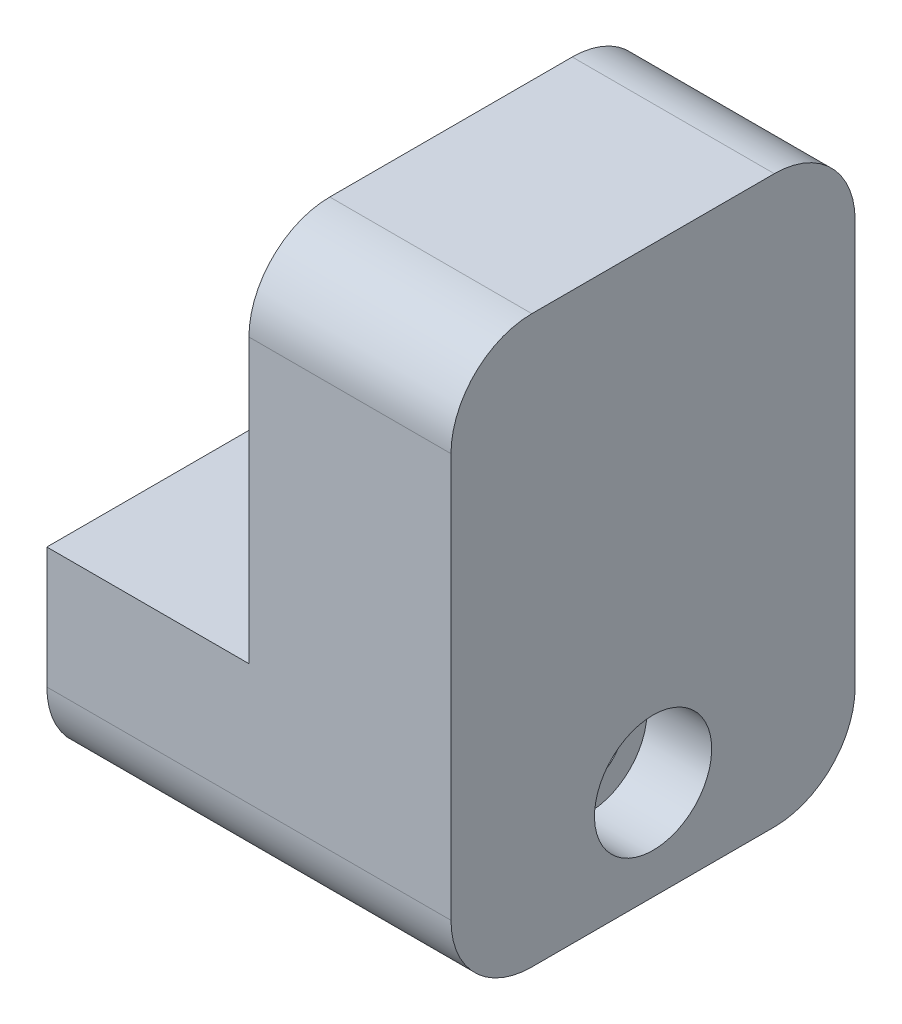
SolidWorks part; units mm, degrees
ref_plane "Front Plane" through (0, 0, 0) normal (0, 0, 1) x (1, 0, 0)
ref_plane "Top Plane" through (0, 0, 0) normal (0, 1, 0) x (1, 0, 0)
ref_plane "Right Plane" through (0, 0, 0) normal (1, 0, 0) x (0, 0, -1)
sketch "Profile" plane through (0, 0, 0) normal (0, 0, 1) x (1, 0, 0)
  line L1 (-6.35, 22.86) -> (6.35, 22.86)
  line L2 (-6.35, 22.86) -> (-6.35, 0)
  line L3 (-6.35, 0) -> (6.35, 0)
  line L4 (6.35, 22.86) -> (6.35, 0)
  line L5 (0, 0) -> (6.35, 0)
  line L6 (0, 0) -> (0, -12.7)
  line L7 (0, -12.7) -> (6.35, -12.7)
  line L8 (6.35, 0) -> (6.35, -12.7)
  dimension "D1" = 22.86
  dimension "D2" = 12.7
  dimension "D3" = 6.35
  dimension "D4" = 12.7
extrude "Boss-Extrude1" add sketch "Profile" along normal mid plane 25.4 contours L4 L1 L2 L3 | L8 L3 L6 L7
sketch "Sketch7" plane through (0, 0, 12.7) normal (0, 0, 1) x (1, 0, 0)
  line L0 (0, -12.7) -> (6.35, -12.7) construction
  line L1 (0, 0) -> (-19.05, 0)
  line L2 (0, 0) -> (0, -12.7)
  line L3 (0, -12.7) -> (-19.05, -12.7)
  line L4 (-19.05, 0) -> (-19.05, -12.7)
  line L5 (-6.35, 22.86) -> (-6.35, 0) construction
  dimension "D1" = 12.7
extrude "Boss-Extrude2" add sketch "Sketch7" against normal up to surface (25.4 mm away)
sketch "ScrewHole" plane through (-19.05, 0, 0) normal (-1, 0, 0) x (0, 0, 1)
  line L0 (-12.7, 0) -> (12.7, 0) construction
  circle A0 centre (0, -6.477) radius 2.159
  dimension "D1" = 4.318
  dimension "D2" = 6.477
extrude "Cut-Extrude1" cut sketch "ScrewHole" against normal through all both and the other way through all
sketch "Sketch3" plane through (6.35, 0, 0) normal (1, 0, 0) x (0, 0, -1)
  circle A0 centre (0, -6.477) radius 2.159 construction
  circle A1 centre (0, -6.477) radius 2.159
  circle A2 centre (0, -6.477) radius 3.683
  dimension "D1" = 7.366
extrude "Cut-Extrude2" cut sketch "Sketch3" against normal blind 4.064
sketch "Sketch10" plane through (-6.35, 0, 0) normal (-1, 0, 0) x (0, 0, 1)
  line L0 (-12.7, 22.86) -> (-12.7, 0) construction
  line L1 (-10.16, 17.78) -> (10.16, 17.78) construction
  line L2 (-10.16, 17.78) -> (-10.16, 5.08) construction
  line L3 (-10.16, 5.08) -> (10.16, 5.08) construction
  line L4 (10.16, 17.78) -> (10.16, 5.08) construction
  circle A0 centre (-10.16, 17.78) radius 1.143
  circle A1 centre (10.16, 17.78) radius 1.143
  circle A2 centre (10.16, 5.08) radius 1.143
  circle A3 centre (-10.16, 5.08) radius 1.143
  point P8 (0, 5.08)
  point P12 (-12.7, 11.43)
  point P13 (-10.16, 11.43)
  dimension "D1" = 2.286
  dimension "D2" = 2.286
  dimension "D3" = 2.286
  dimension "D4" = 2.286
  dimension "D5" = 20.32
  dimension "D6" = 12.7
extrude "Cut-Extrude3" cut sketch "Sketch10" against normal blind 7.62
fillet "Fillet6" radius 5.08 4 edges at (-6.35, -12.7, -12.7) (-6.35, -12.7, 12.7) (0, 22.86, -12.7) (0, 22.86, 12.7)
